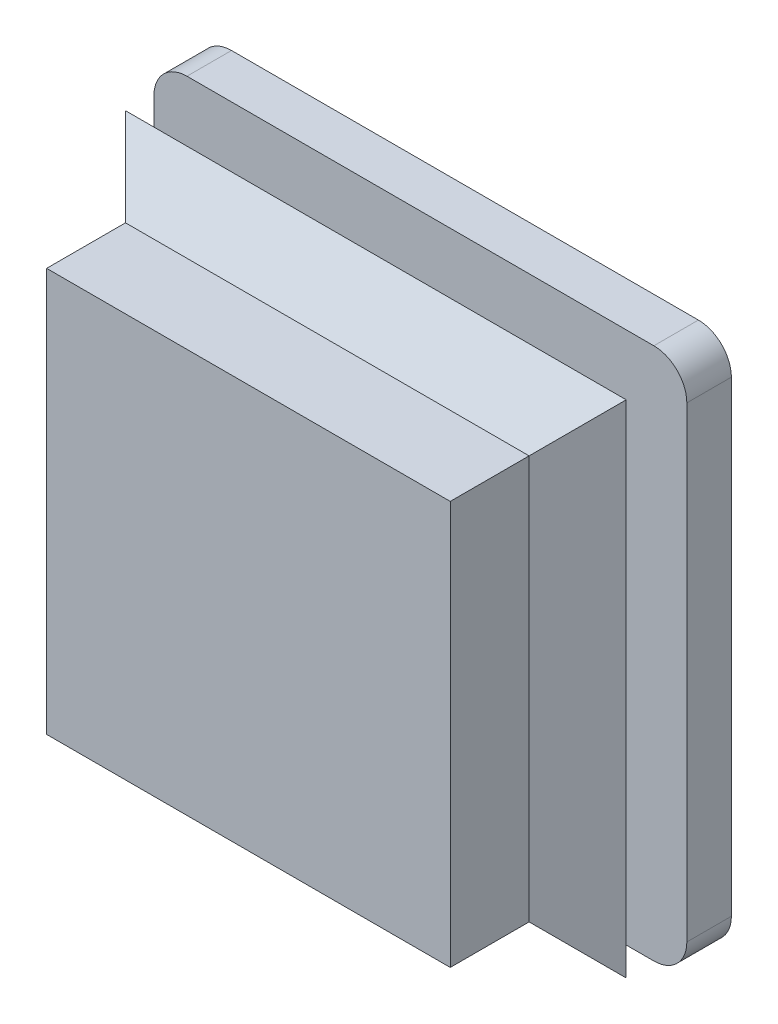
SolidWorks part; units mm, degrees
ref_plane "Plan de face" through (0, 0, 0) normal (0, 0, 1) x (1, 0, 0)
ref_plane "Plan de dessus" through (0, 0, 0) normal (0, 1, 0) x (1, 0, 0)
ref_plane "Plan de droite" through (0, 0, 0) normal (1, 0, 0) x (0, 0, -1)
sketch "Esquisse1" plane through (0, 0, 0) normal (0, 0, 1) x (1, 0, 0)
  line L1 (-29.9, 29.9) -> (29.9, 29.9)
  line L2 (-29.9, 29.9) -> (-29.9, -29.9)
  line L3 (-29.9, -29.9) -> (29.9, -29.9)
  line L4 (29.9, 29.9) -> (29.9, -29.9)
  line L5 (-29.9, 29.9) -> (29.9, -29.9) construction
  line L6 (-29.9, -29.9) -> (29.9, 29.9) construction
  point P0 (0, 0)
  dimension "D1" = 59.8
extrude "Boss.-Extru.1" add sketch "Esquisse1" along normal blind 5
sketch "Esquisse2" plane through (0, 0, 0) normal (0, 0, 1) x (1, 0, 0)
  line L1 (-22.65, 22.65) -> (22.65, 22.65)
  line L2 (-22.65, 22.65) -> (-22.65, -22.65)
  line L3 (-22.65, -22.65) -> (22.65, -22.65)
  line L4 (22.65, 22.65) -> (22.65, -22.65)
  line L5 (-22.65, 22.65) -> (22.65, -22.65) construction
  line L6 (-22.65, -22.65) -> (22.65, 22.65) construction
  point P0 (0, 0)
  dimension "D1" = 45.3
extrude "Boss.-Extru.2" add sketch "Esquisse2" along normal blind 24.3
fillet "Congé1" radius 3.7 4 edges at (29.9, -29.9, 2.5) (-29.9, -29.9, 2.5) (-29.9, 29.9, 2.5) (29.9, 29.9, 2.5)
ref_plane "Plan1" through (0, 0, 10) normal (0, 0, 1) x (1, 0, 0)
sketch "Esquisse6" plane through (0, 0, 10) normal (0, 0, 1) x (1, 0, 0)
  line L1 (-28.1, 28.1) -> (28.1, 28.1)
  line L2 (-28.1, 28.1) -> (-28.1, -28.1)
  line L3 (-28.1, -28.1) -> (28.1, -28.1)
  line L4 (28.1, 28.1) -> (28.1, -28.1)
  line L5 (-28.1, 28.1) -> (28.1, -28.1) construction
  line L6 (-28.1, -28.1) -> (28.1, 28.1) construction
  point P0 (0, 0)
  dimension "D1" = 56.2
extrude "Boss.-Extru.4" add sketch "Esquisse6" along normal blind 10 draft 45
